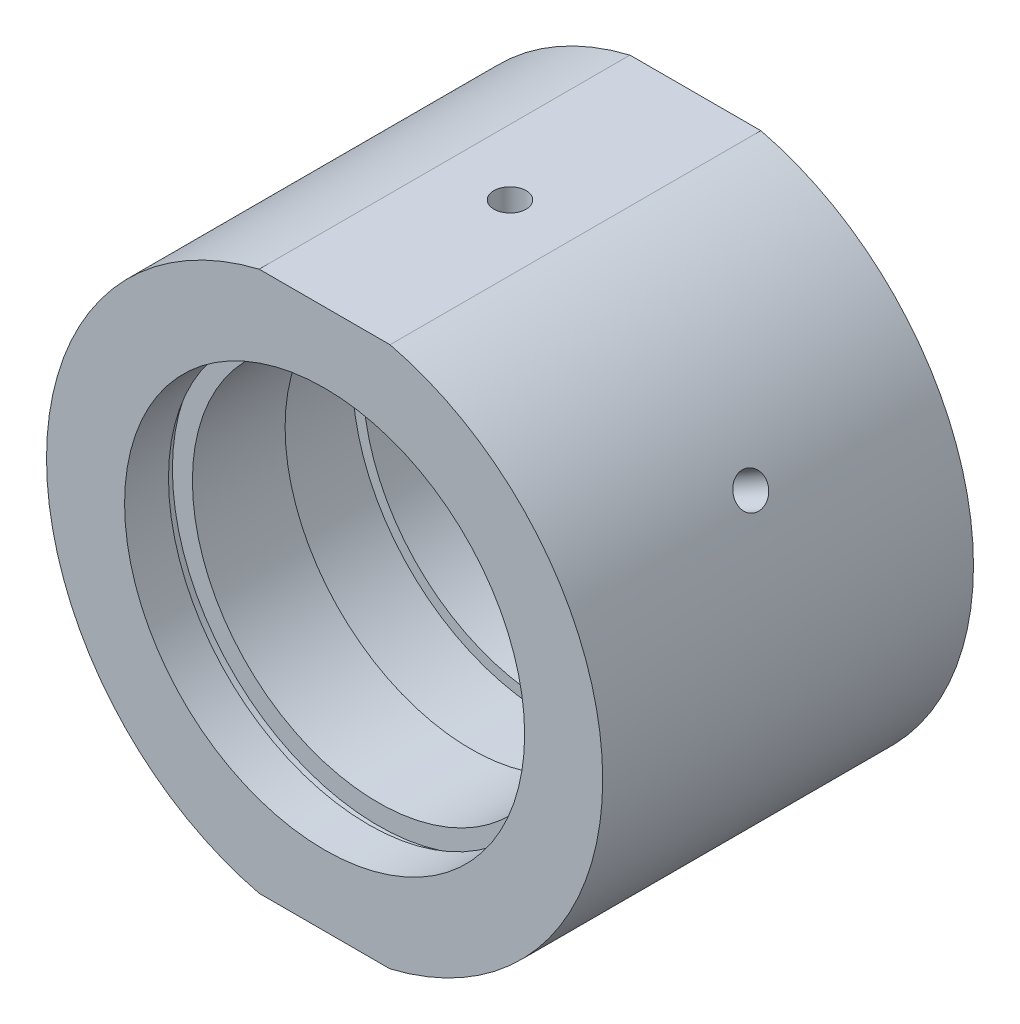
SolidWorks part; units mm, degrees
ref_plane "前视基准面" through (0, 0, 0) normal (0, 0, 1) x (1, 0, 0)
ref_plane "上视基准面" through (0, 0, 0) normal (0, 1, 0) x (1, 0, 0)
ref_plane "右视基准面" through (0, 0, 0) normal (1, 0, 0) x (0, 0, -1)
sketch "草图1" plane through (0, 0, 0) normal (0, 1, 0) x (1, 0, 0)
  line L0 (0, 31.9391) -> (0, -26.491) construction
  line L1 (28.5, 19) -> (28.5, -19)
  line L2 (28.5, -19) -> (20.5, -19)
  line L3 (20.5, -19) -> (20.5, -14.5)
  line L4 (20.5, -14.5) -> (21.1, -14.5)
  line L5 (21.1, -14.5) -> (21.1, -13.5)
  line L6 (21.1, -13.5) -> (19.05, -13.5)
  line L7 (19.05, -13.5) -> (19.05, -4)
  line L8 (19.05, -4) -> (20.15, -4)
  line L9 (20.15, -4) -> (20.15, 4)
  line L10 (20.15, 4) -> (19.05, 4)
  line L11 (19.05, 4) -> (19.05, 13.5)
  line L12 (19.05, 13.5) -> (21.1, 13.5)
  line L13 (21.1, 13.5) -> (21.1, 14.5)
  line L14 (21.1, 14.5) -> (20.5, 14.5)
  line L15 (20.5, 14.5) -> (20.5, 19)
  line L16 (20.5, 19) -> (28.5, 19)
  line L17 (28.5, 0) -> (-5.0345, 0) construction
  point P6 (20.15, 0)
  dimension "D1" = 38
  dimension "D2" = 20.15
  dimension "D3" = 19.05
  dimension "D4" = 19.05
  dimension "D5" = 21.1
  dimension "D6" = 21.1
  dimension "D7" = 20.5
  dimension "D8" = 20.5
  dimension "D9" = 28.5
  dimension "D10" = 1
  dimension "D11" = 1
  dimension "D12" = 5.5
  dimension "D13" = 5.5
  dimension "D14" = 8
  dimension "D15" = 4
  dimension "D16" = 19
  dimension "D17" = 15
  dimension "D18" = 0
revolve "旋转1" add sketch "草图1" angle 360 about L0
cosmetic thread "装饰螺纹线4" parameters "D1"=4.4999, "D2"=42
cosmetic thread "装饰螺纹线5" parameters "D1"=8, "D2"=42
sketch "草图2" plane through (0, 0, 19) normal (0, 0, 1) x (1, 0, 0)
  line L0 (0, 0) -> (43.1523, 0) construction
  line L1 (-33.152, 36.9489) -> (30.8698, 36.9489)
  line L2 (-33.152, 36.9489) -> (-33.152, 27.7)
  line L3 (-33.152, 27.7) -> (30.8698, 27.7)
  line L4 (30.8698, 36.9489) -> (30.8698, 27.7)
  line L5 (30.8698, -36.9489) -> (30.8698, -27.7)
  line L6 (-33.152, -27.7) -> (30.8698, -27.7)
  line L7 (-33.152, -36.9489) -> (-33.152, -27.7)
  line L8 (-33.152, -36.9489) -> (30.8698, -36.9489)
  circle A1 centre (0, 0) radius 28.5 construction
  dimension "D1" = 27.7
  dimension "D2" = 0.8
extrude "切除-拉伸1" cut sketch "草图2" against normal blind 49
sketch "草图10" plane through (0, 0, 0) normal (0, 0, 1) x (1, 0, 0)
  line L0 (0, 27.7) -> (0, -27.7)
  line L1 (6.7052, 27.7) -> (-6.7052, 27.7) construction
  line L2 (-6.7052, -27.7) -> (6.7052, -27.7) construction
  line L3 (0, 0) -> (-24.6817, 14.25)
  line L4 (0, 0) -> (24.6817, 14.25)
  line L5 (-28.5, 0) -> (0, 27.7)
  line L6 (0, -27.7) -> (3.1773, -27.7)
  circle A0 centre (0, 0) radius 28.5 construction
  circle A1 centre (0, 0) radius 28.5 construction
  arc A2 (-28.5, 0) -> (-24.6817, 14.25) centre (0, 0) ccw
  arc A3 (24.6817, 14.25) -> (-28.5, 0) centre (0, 0) ccw
  dimension "D1" = 60
  dimension "D2" = 60
hole_wizard "M4 螺纹孔2" positions "草图15" profile "草图16" tap size "M4" standard "ISO"
sketch "草图15" plane through (0, 27.7, 0) normal (0, 1, 0) x (1, 0, 0)
  point P0 (0, 0)
sketch "草图16" plane through (0, 27.7, 0) normal (1, 0, 0) x (0, 0, 1)
  line L0 (0, 0) -> (0, 6.4914)
  line L1 (0, 6.4914) -> (1.65, 5.5)
  line L2 (1.65, 5.5) -> (1.65, 0)
  line L5 (1.65, 0) -> (0, 0)
  line L10 (0, 6.4914) -> (-1.65, 5.5) construction
  line L11 (0, -6.35) -> (0, 107.95) construction
  dimension "螺纹孔钻头直径" = 3.3
  dimension "螺纹孔钻头深度" = 5.5
  dimension "导头角度" = 118
cosmetic thread "孔螺蚊线3" parameters "D1"=5.5, "D2"=4
hole_wizard "M6 螺纹孔2" positions "草图17" profile "草图18" tap size "M6" standard "ISO"
sketch "草图17" plane through (0, -27.7, 0) normal (0, -1, 0) x (-1, 0, 0)
  point P0 (0, 0)
sketch "草图18" plane through (0, -27.7, 0) normal (1, 0, 0) x (0, 0, -1)
  line L0 (0, 0) -> (0, 7.0022)
  line L1 (0, 7.0022) -> (2.5, 5.5)
  line L2 (2.5, 5.5) -> (2.5, 0)
  line L5 (2.5, 0) -> (0, 0)
  line L10 (0, 7.0022) -> (-2.5, 5.5) construction
  line L11 (0, -6.35) -> (0, 107.95) construction
  dimension "螺纹孔钻头直径" = 5
  dimension "螺纹孔钻头深度" = 5.5
  dimension "导头角度" = 118
cosmetic thread "孔螺蚊线4" parameters "D1"=5.5, "D2"=6
hole_wizard "M4 螺纹孔3" positions "3D草图10" profile "草图19" tap size "M4" standard "ISO"
sketch3d "3D草图10"
  point P0 (24.6817, 14.25, 0)
  point P3 (-24.6817, 14.25, 0)
  point P6 (-24.6817, 14.25, 0)
  point P8 (-24.6817, 14.25, 0)
  point P12 (24.6817, 14.25, 0)
  point P15 (24.6817, 14.25, 0)
cosmetic thread "孔螺蚊线5" parameters "D1"=8, "D2"=4
sketch "草图19" plane through (24.6817, 14.25, 0) normal (0, 0, 1) x (-0.5, 0.866, 0)
  line L0 (0, 0) -> (0, 11.0914)
  line L1 (0, 11.0914) -> (1.65, 10.1)
  line L2 (1.65, 10.1) -> (1.65, 0)
  line L5 (1.65, 0) -> (0, 0)
  line L10 (0, 11.0914) -> (-1.65, 10.1) construction
  line L11 (0, -6.35) -> (0, 107.95) construction
  dimension "螺纹孔钻头直径" = 3.3
  dimension "螺纹孔钻头深度" = 10.1
  dimension "导头角度" = 118
cosmetic thread "孔螺蚊线6" parameters "D1"=8, "D2"=4
